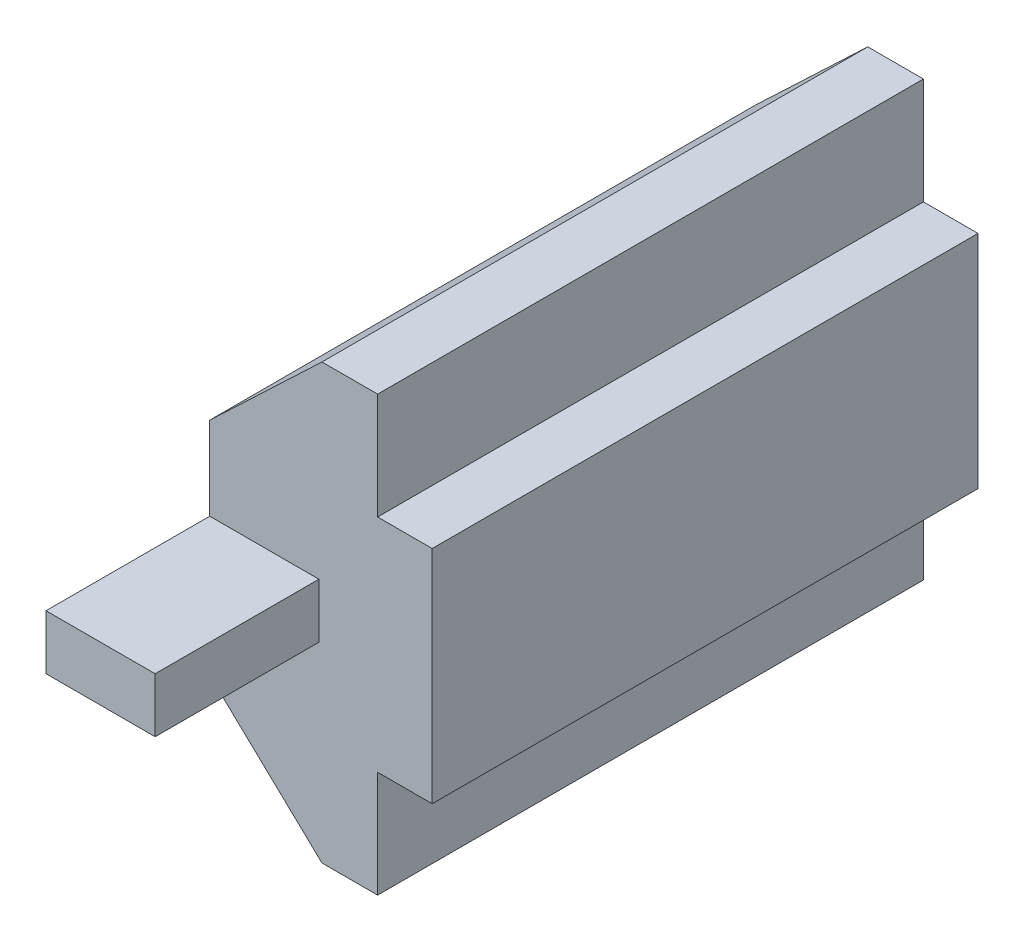
SolidWorks part; units mm, degrees
ref_plane "Front Plane" through (0, 0, 0) normal (0, 0, 1) x (1, 0, 0)
ref_plane "Top Plane" through (0, 0, 0) normal (0, 1, 0) x (1, 0, 0)
ref_plane "Right Plane" through (0, 0, 0) normal (1, 0, 0) x (0, 0, -1)
sketch "Sketch2" plane through (0, 0, 0) normal (0, 0, 1) x (1, 0, 0)
  line L0 (0, 4.05) -> (2, 4.05)
  line L1 (2, 4.05) -> (2, -4.05)
  line L2 (2, -4.05) -> (0, -4.05)
  line B0 (0, -7.95) -> (-2.04, -7.95)
  line B1 (-6.1524, -4.048) -> (-6.1524, 4.048)
  line B2 (-2.04, 7.95) -> (0, 7.95)
  line B3 (0, 7.95) -> (0, -7.95)
  line B4 (-2.04, -7.95) -> (-6.1524, -4.048)
  line B5 (-6.1524, 4.048) -> (-2.04, 7.95)
  line B6 (0, -4.05) -> (0, 4.05) construction
  dimension "D1" = 2
sketch_block_instance "Extrusion Profile-2"
sketch_block "Block1" parameters "D1"=8.44, "D2"=2.6, "D3"=6, "D4"=16.7, "D6"=5.6686, "D7"=2.0404, "D8"=8.0963, "D9"=15.9, "D5"=2.4157
extrude "Boss-Extrude1" add sketch "Sketch2" along normal blind 20 contours B2 B5 B1 B4 B0 B3 | L0 B3 L2 L1
sketch "Sketch3" plane through (0, 0, 20) normal (0, 0, 1) x (1, 0, 0)
  line L0 (-6.1524, 1) -> (-6.1524, -1)
  line L1 (-6.1524, -4.048) -> (-6.1524, 4.048) construction
  line L2 (-6.1524, -1) -> (-2.1524, -1)
  line L3 (-2.1524, -1) -> (-2.1524, 1)
  line L4 (-2.1524, 1) -> (-6.1524, 1)
  point P0 (0, 0)
  point P5 (-6.1524, 0)
  dimension "D1" = 2
  dimension "D2" = 4
extrude "Boss-Extrude2" add sketch "Sketch3" along normal blind 6
